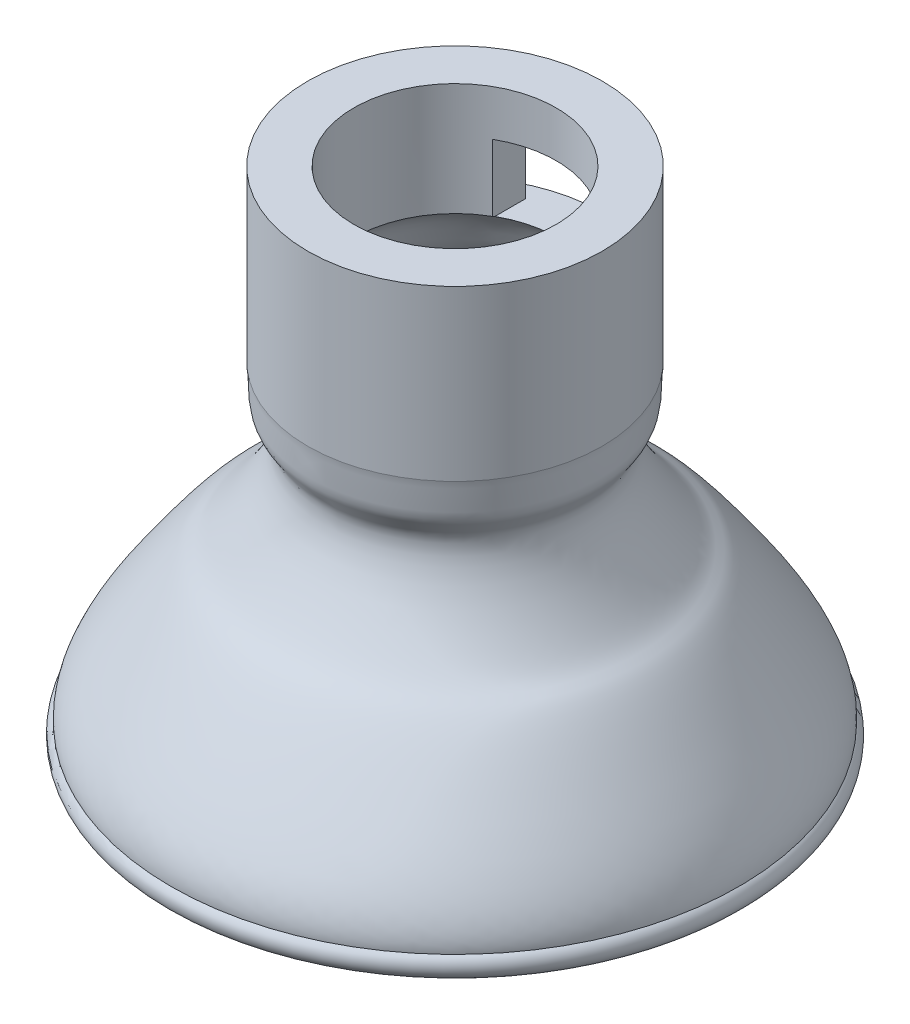
SolidWorks part; units mm, degrees
material "ABS"
ref_plane "Plano frontal" through (0, 0, 0) normal (0, 0, 1) x (1, 0, 0)
ref_plane "Plano superior" through (0, 0, 0) normal (0, 1, 0) x (1, 0, 0)
ref_plane "Plano direito" through (0, 0, 0) normal (1, 0, 0) x (0, 0, -1)
sketch "Esboço1" plane through (0, 0, 0) normal (0, 0, 1) x (1, 0, 0)
  line L1 (12.4936, 41.6466) -> (12.4936, 41.4599)
  line L2 (8.5759, 46.237) -> (8.5759, 55.7804)
  line L3 (0, 44.5174) -> (0, 20.7069) construction
  line L4 (0, -55) -> (0, 55) construction
  line L5 (8.5759, 55.7804) -> (12.4936, 55.7804)
  line L6 (12.4936, 46.237) -> (12.4936, 55.7804)
  line L7 (12.4936, 46.237) -> (12.4936, 41.6466)
  arc A0 (22.8836, 15.0236) -> (24.0786, 14.9142) centre (23.3968, 14.0472) ccw
  spline S0 degree 3 poles (12.4936, 41.4599) (12.3013, 40.1984) (12.6727, 38.2323) (9.8982, 35.8696) (14.8595, 27.8084) (16.0899, 28.0208) (19.3542, 24.143) (24.2566, 16.8596) (24.0786, 14.9142) knots 0 0 0 0 0.101005 0.17504 0.372875 0.603292 0.835962 1 1 1 1
  spline S1 degree 1 poles (11.3073, 41.6408) (22.8836, 15.0236) knots 0 0 1 1 construction
  spline S2 degree 3 poles (11.3073, 41.6408) (11.2735, 41.4191) (11.2251, 40.9574) (11.193, 40.1522) (11.194, 39.3041) (11.1106, 38.7771) (11.0298, 38.5851) (10.8756, 38.3307) (10.6328, 37.9932) (10.3379, 37.5542) (10.0436, 36.9657) (9.826, 36.0076) (9.9146, 34.8903) (10.2965, 33.5753) (10.8639, 32.2936) (11.7591, 30.6645) (12.9464, 28.9199) (13.9488, 27.6965) (14.8014, 26.9604) (15.4187, 26.5771) (15.8418, 26.2557) (16.5896, 25.4893) (17.6296, 24.2205) (19.0007, 22.3695) (20.5444, 20.2008) (21.7129, 18.3359) (22.303, 17.2067) (22.6379, 16.3823) (22.8087, 15.8292) (22.8908, 15.3468) (22.8943, 15.1404) (22.8836, 15.0236) knots 0 0 0 0 0.015625 0.03125 0.0625 0.09375 0.109375 0.125 0.140625 0.15625 0.171875 0.1875 0.21875 0.25 0.28125 0.3125 0.375 0.4375 0.5 0.5625 0.625 0.6875 0.75 0.8125 0.875 0.90625 0.9375 0.953125 0.96875 0.984375 1 1 1 1
  spline S3 degree 3 poles (11.3073, 41.6408) (10.4933, 43.2397) (10.3322, 45.294) (8.5759, 46.237) knots 0 0 0 0 1 1 1 1
  dimension "D1" = 1.2
revolve "Revolução1" add sketch "Esboço1" angle 360 about L3
sketch "Esboço2" plane through (0, 0, 0) normal (0, 0, 1) x (1, 0, 0)
  line L0 (0, -21.0905) -> (0, 21.0905) construction
  line L1 (4.2604, 46.1353) -> (-4.2604, 46.1353)
  line L2 (4.2604, 46.1353) -> (4.2604, 51.8993)
  line L3 (4.2604, 51.8993) -> (-4.2604, 51.8993)
  line L4 (-4.2604, 46.1353) -> (-4.2604, 51.8993)
  line L5 (4.2604, 46.1353) -> (-4.2604, 51.8993) construction
  line L6 (4.2604, 51.8993) -> (-4.2604, 46.1353) construction
  point P0 (0, 49.0173)
extrude "Corte-extrusão1" cut sketch "Esboço2" against normal blind 21
sketch "Esboço3" plane through (0, 0, 0) normal (1, 0, 0) x (0, 0, -1)
  line L1 (12.4936, 51.8993) -> (10.2498, 51.8993)
  line L2 (12.4936, 51.8993) -> (12.4936, 46.1353)
  line L3 (12.4936, 46.1353) -> (10.2498, 46.1353)
  line L4 (10.2498, 51.8993) -> (10.2498, 46.1353)
extrude "Corte-extrusão2" cut sketch "Esboço3" against normal blind 21 and the other way blind 21
